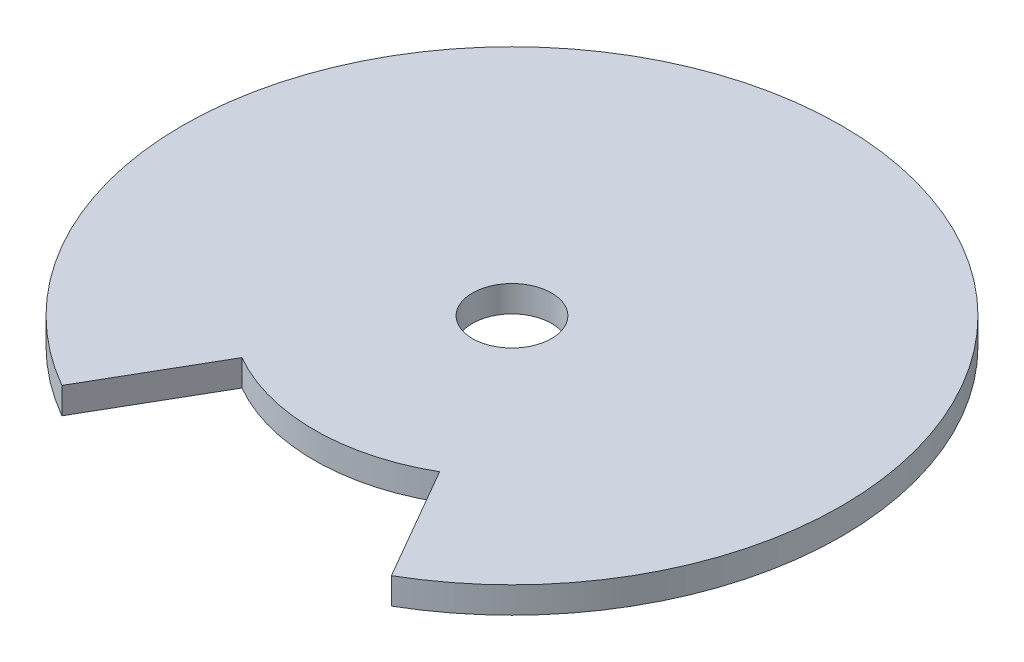
SolidWorks part; units mm, degrees
ref_plane "Спереди" through (0, 0, 0) normal (0, 0, 1) x (1, 0, 0)
ref_plane "Сверху" through (0, 0, 0) normal (0, 1, 0) x (1, 0, 0)
ref_plane "Справа" through (0, 0, 0) normal (1, 0, 0) x (0, 0, -1)
sketch "Эскиз1" plane through (0, 0, 0) normal (0, 1, 0) x (1, 0, 0)
  line L0 (0, 0) -> (0, -21.8403) construction
  line L1 (0, 0) -> (-12.5, -21.6506)
  line L2 (0, 0) -> (12.5, -21.6506)
  circle A0 centre (0, 0) radius 25
  circle A1 centre (0, 0) radius 3
  circle A2 centre (0, 0) radius 15
  dimension "D1" = 50
  dimension "D2" = 6
  dimension "D4" = 60
  dimension "D5" = 30
  dimension "D3" = 10
extrude "Бобышка-Вытянуть1" add sketch "Эскиз1" along normal blind 2 contours A2 L2 A0 L1 | L2 A2 L1 A1 | L0 A1 L1 A2 | A1 L0 A2 L2
